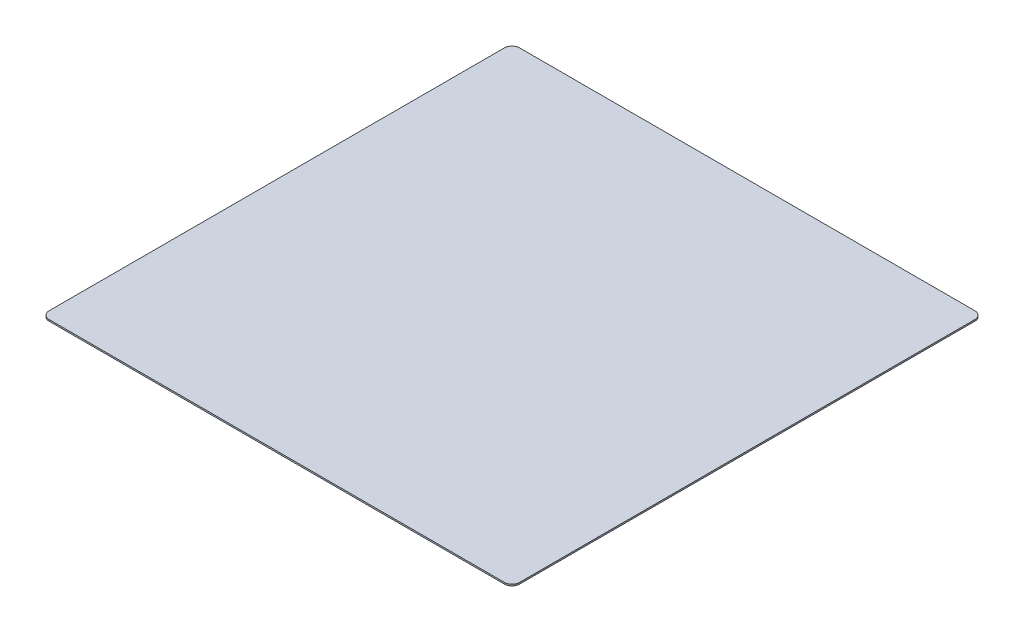
SolidWorks part; units mm, degrees
material "普通碳钢"
ref_plane "前视基准面" through (0, 0, 0) normal (0, 0, 1) x (1, 0, 0)
ref_plane "上视基准面" through (0, 0, 0) normal (0, 1, 0) x (1, 0, 0)
ref_plane "右视基准面" through (0, 0, 0) normal (1, 0, 0) x (0, 0, -1)
sketch "草图1" plane through (0, 0, 0) normal (0, 1, 0) x (1, 0, 0)
  line L1 (-150, 155) -> (150, 155)
  line L2 (-155, 150) -> (-155, -150)
  line L3 (-150, -155) -> (150, -155)
  line L4 (155, 150) -> (155, -150)
  line L5 (-155, 155) -> (155, -155) construction
  line L6 (-155, -155) -> (155, 155) construction
  arc A0 (-155, -150) -> (-150, -155) centre (-150, -150) ccw
  arc A1 (150, -155) -> (155, -150) centre (150, -150) ccw
  arc A2 (155, 150) -> (150, 155) centre (150, 150) ccw
  arc A3 (-150, 155) -> (-155, 150) centre (-150, 150) ccw
  point P0 (0, 0)
  dimension "D3" = 5
  dimension "D1" = 310
  dimension "D2" = 310
extrude "凸台-拉伸1" add sketch "草图1" along normal blind 1
